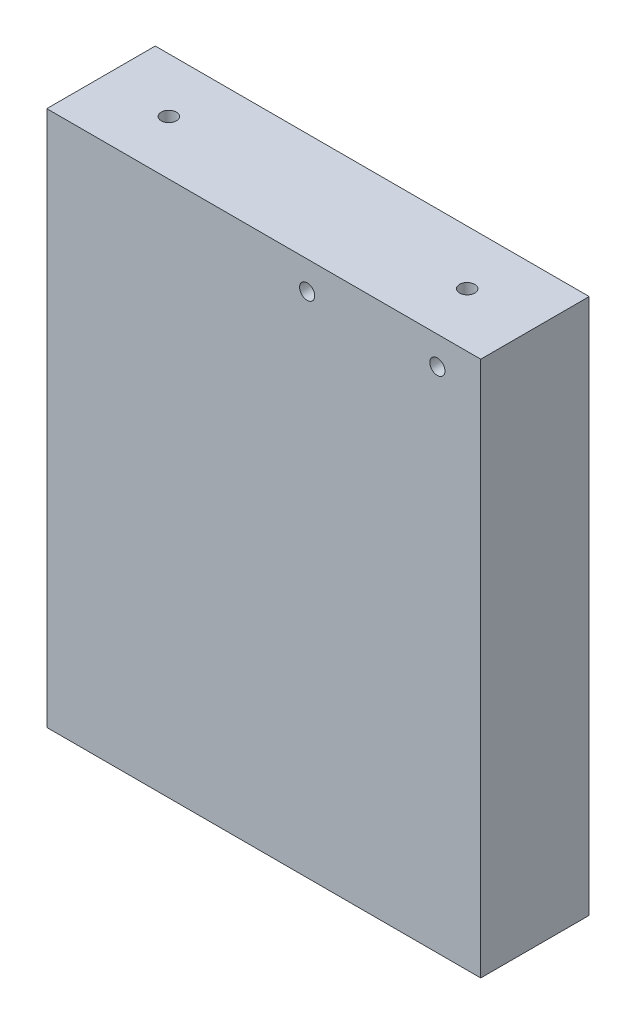
SolidWorks part; units mm, degrees
ref_plane "Front Plane" through (0, 0, 0) normal (0, 0, 1) x (1, 0, 0)
ref_plane "Top Plane" through (0, 0, 0) normal (0, 1, 0) x (1, 0, 0)
ref_plane "Right Plane" through (0, 0, 0) normal (1, 0, 0) x (0, 0, -1)
sketch "Sketch1" plane through (0, 0, 0) normal (0, 1, 0) x (1, 0, 0)
  line L1 (0, 0) -> (50.8, 0)
  line L2 (0, 0) -> (0, -12.7)
  line L3 (0, -12.7) -> (50.8, -12.7)
  line L4 (50.8, 0) -> (50.8, -12.7)
  dimension "D1" = 50.8
  dimension "D2" = 12.7
extrude "Boss-Extrude1" add sketch "Sketch1" along normal blind 62.738
sketch "Sketch2" plane through (0, 0, 0) normal (0, -1, 0) x (1, 0, 0)
  line L0 (0, 0) -> (0, 12.7) construction
  line L1 (50.8, 12.7) -> (50.8, 0) construction
  point P0 (6.35, 6.35)
  point P1 (44.45, 6.35)
  point P6 (0, 6.35)
  dimension "D1" = 38.1
  dimension "D2" = 6.35
hole_wizard "#8-32 Tapped Hole1" positions "Sketch3" profile "Sketch4" tap size "#8-32" standard "ANSI Inch"
sketch "Sketch3" plane through (0, 0, 0) normal (0, -1, 0) x (-1, 0, 0)
  point P0 (-6.35, -6.35)
  point P3 (-44.45, -6.35)
sketch "Sketch4" plane through (6.35, 0, 6.35) normal (1, 0, 0) x (0, 0, -1)
  line L0 (0, 0) -> (0, 18.6654)
  line L1 (0, 18.6654) -> (1.7272, 17.6276)
  line L2 (1.7272, 17.6276) -> (1.7272, 0)
  line L5 (1.7272, 0) -> (0, 0)
  line L10 (0, 18.6654) -> (-1.7272, 17.6276) construction
  line L11 (0, -6.35) -> (0, 107.95) construction
  dimension "Tap Drill Dia." = 3.4544
  dimension "Tap Drill Depth" = 17.6276
  dimension "Drill Angle" = 118
cosmetic thread "Hole Thread1" parameters "D1"=15.24, "D2"=4.1656
cosmetic thread "Hole Thread2" parameters "D1"=15.24, "D2"=4.1656
sketch "Sketch5" plane through (0, 62.738, 0) normal (0, 1, 0) x (1, 0, 0)
  line L0 (0, 0) -> (0, -12.7) construction
  point P1 (7.9375, -6.35)
  point P2 (42.8625, -6.35)
  point P6 (0, -6.35)
  dimension "D1" = 34.925
  dimension "D2" = 7.9375
hole_wizard "#2-56 Tapped Hole1" positions "Sketch8" profile "Sketch9" tap size "#2-56" standard "ANSI Inch"
sketch "Sketch8" plane through (0, 62.738, 0) normal (0, 1, 0) x (1, 0, 0)
  point P0 (7.9375, -6.35)
  point P3 (42.8625, -6.35)
sketch "Sketch9" plane through (7.9375, 62.738, 6.35) normal (1, 0, 0) x (0, 0, 1)
  line L0 (0, 0) -> (0, 13.2342)
  line L1 (0, 13.2342) -> (0.889, 12.7)
  line L2 (0.889, 12.7) -> (0.889, 0)
  line L5 (0.889, 0) -> (0, 0)
  line L10 (0, 13.2342) -> (-0.889, 12.7) construction
  line L11 (0, -6.35) -> (0, 107.95) construction
  dimension "Tap Drill Dia." = 1.778
  dimension "Tap Drill Depth" = 12.7
  dimension "Drill Angle" = 118
sketch "Sketch10" plane through (0, 0, 12.7) normal (0, 0, 1) x (1, 0, 0)
  line L0 (0, 62.738) -> (50.8, 62.738) construction
  line L2 (50.8, 62.738) -> (50.8, 0) construction
  point P0 (30.48, 59.436)
  point P1 (45.72, 59.436)
  dimension "D1" = 3.302
  dimension "D2" = 3.302
  dimension "D3" = 5.08
  dimension "D4" = 15.24
hole_wizard "#2-56 Tapped Hole2" positions "Sketch11" profile "Sketch12" tap size "#2-56" standard "ANSI Inch"
sketch "Sketch11" plane through (0, 0, 12.7) normal (0, 0, 1) x (1, 0, 0)
  point P0 (30.48, 59.436)
  point P3 (45.72, 59.436)
cosmetic thread "Hole Thread3" parameters "D1"=9.4488, "D2"=2.1844
cosmetic thread "Hole Thread4" parameters "D1"=9.4488, "D2"=2.1844
sketch "Sketch12" plane through (30.48, 59.436, 12.7) normal (1, 0, 0) x (0, -1, 0)
  line L0 (0, 0) -> (0, 11.3546)
  line L1 (0, 11.3546) -> (0.889, 10.8204)
  line L2 (0.889, 10.8204) -> (0.889, 0)
  line L5 (0.889, 0) -> (0, 0)
  line L10 (0, 11.3546) -> (-0.889, 10.8204) construction
  line L11 (0, -6.35) -> (0, 107.95) construction
  dimension "Tap Drill Dia." = 1.778
  dimension "Tap Drill Depth" = 10.8204
  dimension "Drill Angle" = 118
